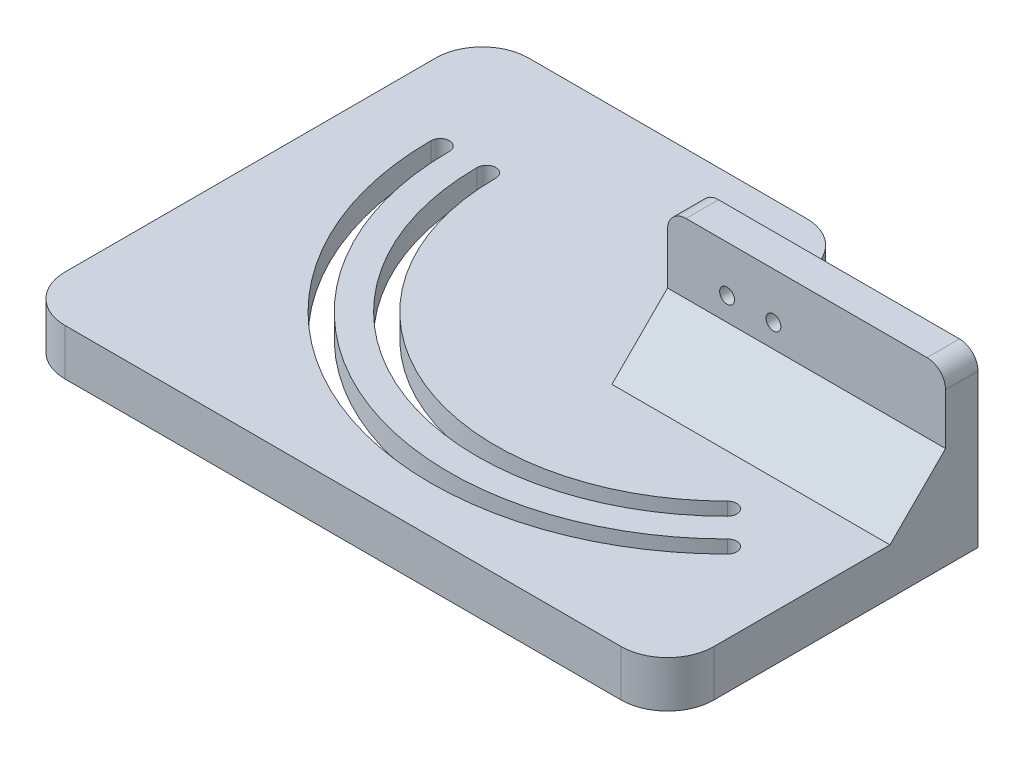
SolidWorks part; units mm, degrees
ref_plane "Front Plane" through (0, 0, 0) normal (0, 0, 1) x (1, 0, 0)
ref_plane "Top Plane" through (0, 0, 0) normal (0, 1, 0) x (1, 0, 0)
ref_plane "Right Plane" through (0, 0, 0) normal (1, 0, 0) x (0, 0, -1)
sketch "Sketch1" plane through (0, 0, 0) normal (0, 1, 0) x (1, 0, 0)
  line L1 (0, 0) -> (170, 0)
  line L2 (0, 0) -> (0, 120)
  line L3 (0, 120) -> (170, 120)
  line L4 (170, 0) -> (170, 120)
extrude "Boss-Extrude1" add sketch "Sketch1" along normal blind 10
sketch "Sketch2" plane through (0, 10, 0) normal (0, 1, 0) x (1, 0, 0)
  line L0 (170, 120) -> (170, 80)
  line L1 (170, 0) -> (170, 120) construction
  line L2 (170, 80) -> (110, 80)
  line L3 (110, 80) -> (110, 120)
  line L4 (170, 120) -> (0, 120) construction
  line L5 (110, 120) -> (170, 120)
extrude "Boss-Extrude2" add sketch "Sketch2" along normal blind 2
sketch "Sketch3" plane through (0, 12, 0) normal (0, 1, 0) x (1, 0, 0)
  line L6 (170, 80) -> (110, 80)
  line L7 (110, 80) -> (110, 88)
  line L8 (110, 120) -> (110, 80) construction
  line L9 (110, 88) -> (170, 88)
  line L10 (170, 80) -> (170, 120) construction
  line L11 (170, 88) -> (170, 80)
extrude "Boss-Extrude3" add sketch "Sketch3" along normal blind 25
sketch "Sketch4" plane through (0, 0, -88) normal (0, 0, -1) x (-1, 0, 0)
  line L0 (-132.8549, 27) -> (-122.8549, 27) construction
  line L2 (-170, 37) -> (-110, 37) construction
  circle A1 centre (-132.8549, 27) radius 1.6
  circle A2 centre (-122.8549, 27) radius 1.6
  dimension "D1" = 10
extrude "Cut-Extrude1" cut sketch "Sketch4" against normal blind 10
sketch "Sketch5" plane through (0, 10, 0) normal (0, 1, 0) x (1, 0, 0)
  arc A16 (44.9348, 94) -> (154.1897, 48.7452) centre (108.9348, 94) ccw
  arc A17 (48.9348, 94) -> (151.3612, 51.5736) centre (108.9348, 94) ccw
  arc A18 (48.9348, 94) -> (44.9348, 94) centre (46.9348, 94) ccw
  arc A19 (154.1897, 48.7452) -> (151.3612, 51.5736) centre (152.7755, 50.1594) ccw
  arc A21 (58.9348, 94) -> (144.2902, 58.6447) centre (108.9348, 94) ccw
  arc A22 (54.9348, 94) -> (147.1186, 55.8162) centre (108.9348, 94) ccw
  arc A23 (58.9348, 94) -> (54.9348, 94) centre (56.9348, 94) ccw
  arc A24 (147.1186, 55.8162) -> (144.2902, 58.6447) centre (145.7044, 57.2304) ccw
extrude "Cut-Extrude2" cut sketch "Sketch5" against normal blind 36
chamfer "Chamfer1" distance 12 angle 45 1 edges at (140, 10, -80)
fillet "Fillet4" radius 4 2 edges at (170, 37, -84) (110, 37, -84)
chamfer "Chamfer2" distance 3 angle 45 1 edges at (140, 12, -88)
sketch "Sketch7" plane through (0, 0, 0) normal (0, -1, 0) x (1, 0, 0)
  arc A0 (140.7546, -62.1802) -> (63.9348, -94) centre (108.9348, -94) ccw
  arc A1 (157.7252, -45.2096) -> (39.9348, -94) centre (108.9348, -94) ccw
  arc A2 (39.9348, -94) -> (63.9348, -94) centre (51.9348, -94) ccw
  arc A3 (140.7546, -62.1802) -> (157.7252, -45.2096) centre (149.2399, -53.6949) ccw
extrude "Cut-Extrude4" cut sketch "Sketch7" against normal blind 5
sketch "Sketch8" plane through (0, 10, 0) normal (0, 1, 0) x (1, 0, 0)
  line L0 (110, 120) -> (0, 120) construction
  line L1 (0, 0) -> (30, 0)
  line L2 (0, 0) -> (0, 120)
  line L3 (0, 120) -> (30, 120)
  line L4 (30, 20) -> (30, 120)
  line L5 (170, 0) -> (170, 20)
  line L6 (170, 0) -> (170, 68) construction
  line L7 (170, 20) -> (30, 20)
  line L8 (170, 0) -> (30, 0)
extrude "Cut-Extrude5" cut sketch "Sketch8" against normal blind 19
fillet "Fillet5" radius 10 5 edges at (30, 5, -120) (170, 6, -120) (110, 11, -120) (30, 5, -20) (170, 5, -20)
sketch "Sketch9" plane through (0, 37, 0) normal (0, 1, 0) x (1, 0, 0)
  line L0 (170, 88) -> (170, 87)
  line L1 (170, 88) -> (170, 80) construction
  line L2 (170, 87) -> (110, 87)
  line L3 (110, 110) -> (110, 68) construction
  line L4 (110, 87) -> (110, 138.4354)
  line L5 (110, 138.4354) -> (206.6941, 135.3103)
  line L6 (206.6941, 135.3103) -> (170, 88)
extrude "Cut-Extrude6" cut sketch "Sketch9" against normal blind 91
fillet "Fillet6" radius 10 2 edges at (110, 5, -87) (110, 5, -120)
